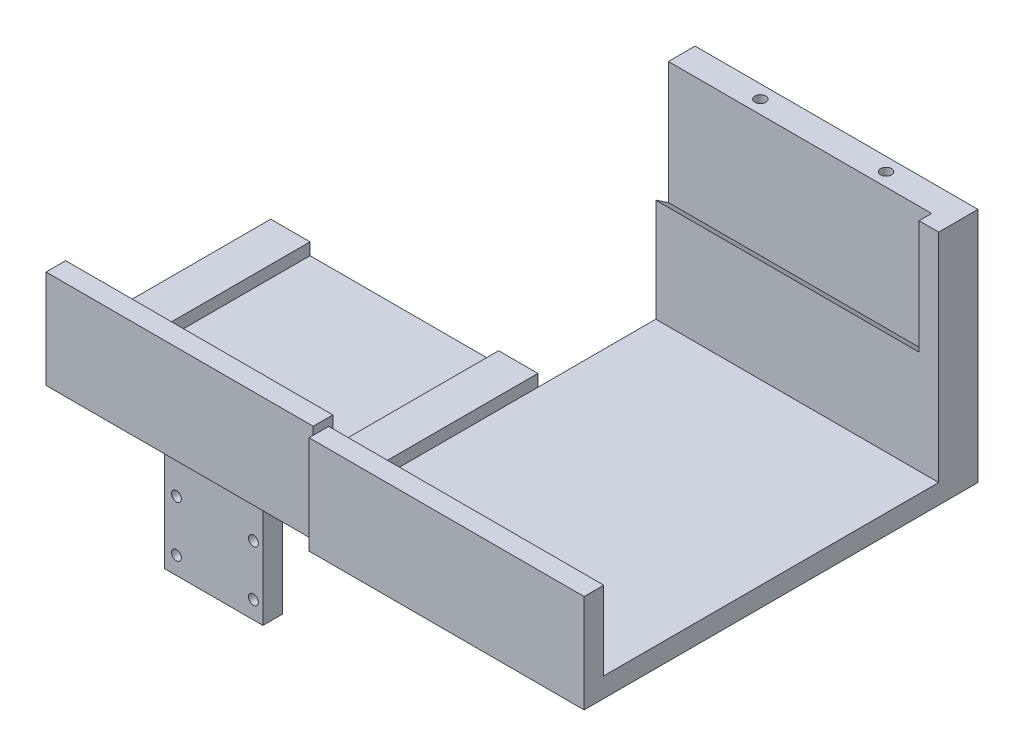
SolidWorks part; units mm, degrees
ref_plane "Front Plane" through (0, 0, 0) normal (0, 0, 1) x (1, 0, 0)
ref_plane "Top Plane" through (0, 0, 0) normal (0, 1, 0) x (1, 0, 0)
ref_plane "Right Plane" through (0, 0, 0) normal (1, 0, 0) x (0, 0, -1)
sketch "Sketch1" plane through (0, 0, 0) normal (0, 1, 0) x (1, 0, 0)
  line L1 (0, 0) -> (25, 0)
  line L2 (0, 0) -> (0, 38)
  line L3 (0, 38) -> (25, 38)
  line L4 (25, 0) -> (25, 38)
  dimension "D1" = 38
  dimension "D2" = 25
extrude "Boss-Extrude1" add sketch "Sketch1" along normal blind 12
ref_plane "Plane1" through (0, 0, -19) normal (0, 0, 1) x (1, 0, 0)
sketch "Sketch3" plane through (0, 0, 0) normal (0, 0, 1) x (1, 0, 0)
  line L1 (0, 12) -> (25, 12)
  line L2 (0, 12) -> (0, 0)
  line L3 (0, 0) -> (25, 0)
  line L4 (25, 12) -> (25, 0)
extrude "Boss-Extrude2" add sketch "Sketch3" along normal blind 5.5
sketch "Sketch5" plane through (0, 0, 0) normal (0, -1, 0) x (1, 0, 0)
  line L0 (25, 5.5) -> (25, -38) construction
  line L1 (0, 5.5) -> (25, 5.5)
  line L2 (0, 5.5) -> (0, 0.5)
  line L3 (0, 0.5) -> (25, 0.5)
  line L4 (25, 5.5) -> (25, 0.5)
  dimension "D1" = 5
extrude "Boss-Extrude3" add sketch "Sketch5" along normal blind 21
sketch "Sketch6" plane through (0, 0, 5.5) normal (0, 0, 1) x (1, 0, 0)
  line L0 (0, 12) -> (0, -21) construction
  line L2 (25, -21) -> (0, -21) construction
  circle A0 centre (3, -16.5) radius 1.25
  circle A1 centre (22.59, -16.5) radius 1.25
  circle A2 centre (22.59, -3.53) radius 1.25
  circle A3 centre (3, -3.53) radius 1.25
  dimension "D2" = 2.5
  dimension "D3" = 2.5
  dimension "D4" = 2.5
  dimension "D5" = 2.5
  dimension "D1" = 3
  dimension "D6" = 19.59
  dimension "D8" = 4.5
  dimension "D9" = 12.97
  dimension "D12" = 3
extrude "Cut-Extrude1" cut sketch "Sketch6" against normal blind 10
mirror "Mirror1" about plane through (0, 0, -19) normal (0, 0, 1) of "Cut-Extrude1", "Boss-Extrude3", "Boss-Extrude2"
sketch "Sketch7" plane through (0, 12, 0) normal (0, 1, 0) x (1, 0, 0)
  line L0 (12.5, 43.5) -> (12.5, -5.5) construction
  line L4 (0, 19) -> (25, 19) construction
  line L7 (117.5, 74) -> (-92.5, 74)
  line L8 (-92.5, 74) -> (-92.5, -11.25)
  line L9 (-92.5, -11.25) -> (117.5, -11.25)
  line L10 (117.5, -11.25) -> (117.5, 74)
  point P3 (12.5, -5.5)
  point P6 (12.5, 74)
  dimension "D1" = 55
  dimension "D2" = 30.25
  dimension "D3" = 210
extrude "Boss-Extrude4" add sketch "Sketch7" along normal blind 5
sketch "Sketch8" plane through (117.5, 0, 0) normal (1, 0, 0) x (0, 0, -1)
  line L0 (74, 12) -> (74, 72.2)
  line L2 (84, 72.2) -> (84, 12)
  line L3 (84, 12) -> (74, 12)
  line L4 (74, 72.2) -> (84, 72.2)
  dimension "D1" = 10
  dimension "D2" = 60.2
extrude "Boss-Extrude5" add sketch "Sketch8" against normal through all
sketch "Sketch9" plane through (-92.5, 0, 0) normal (-1, 0, 0) x (0, 0, 1)
  line L0 (-74, 43.24) -> (-77, 41.26) construction
  line L1 (-74, 72.2) -> (-74, 17) construction
  line L2 (-77, 41.26) -> (-77, 72.2) construction
  line L3 (-84, 72.2) -> (-74, 72.2) construction
  line L4 (-74, 17) -> (11.25, 17) construction
  line L5 (-74, 43.24) -> (-77.2, 41.128)
  line L6 (-77.2, 41.128) -> (-77.2, 72.2)
  line L7 (-77.2, 72.2) -> (-74, 72.2)
  line L8 (-74, 72.2) -> (-74, 43.24)
  dimension "D1" = 26.24
  dimension "D2" = 3
  dimension "D3" = 24.26
  dimension "D4" = 3.2
extrude "Cut-Extrude3" cut sketch "Sketch9" against normal through all
sketch "Sketch10" plane through (117.5, 0, 0) normal (1, 0, 0) x (0, 0, -1)
  line L0 (77.2, 72.2) -> (74, 72.2)
  line L1 (74, 72.2) -> (74, 43.24)
  line L2 (74, 43.24) -> (77.2, 41.128)
  line L3 (77.2, 41.128) -> (77.2, 72.2)
extrude "Boss-Extrude6" add sketch "Sketch10" against normal blind 5
sketch "Sketch11" plane through (0, 17, 0) normal (0, 1, 0) x (1, 0, 0)
  line L0 (117.5, 74) -> (-92.5, 74) construction
  line L1 (35.5, 74) -> (45.5, 74)
  line L2 (35.5, 74) -> (35.5, -11.25)
  line L3 (35.5, -11.25) -> (45.5, -11.25)
  line L4 (45.5, 74) -> (45.5, -11.25)
  line L5 (-92.5, -11.25) -> (117.5, -11.25) construction
  line L6 (117.5, -11.25) -> (117.5, 74) construction
  line L7 (-22.5, 74) -> (-12.5, 74)
  line L8 (-22.5, 74) -> (-22.5, -11.25)
  line L9 (-22.5, -11.25) -> (-12.5, -11.25)
  line L10 (-12.5, 74) -> (-12.5, -11.25)
  dimension "D1" = 72
  dimension "D2" = 10
  dimension "D3" = 68
  dimension "D4" = 10
extrude "Boss-Extrude7" add sketch "Sketch11" along normal blind 3.05
sketch "Sketch12" plane through (0, 17, 0) normal (0, 1, 0) x (1, 0, 0)
  line L0 (-92.5, 6.375) -> (-92.5, 56.375)
  line L1 (-92.5, 74) -> (-92.5, -11.25) construction
  line L2 (-92.5, 56.375) -> (-82.5, 56.375)
  line L3 (-82.5, 56.375) -> (-82.5, 6.375)
  line L4 (-82.5, 6.375) -> (-92.5, 6.375)
  line L5 (-42.5, 6.375) -> (-42.5, 56.375)
  line L6 (-42.5, 56.375) -> (-32.5, 56.375)
  line L7 (-32.5, 56.375) -> (-32.5, 6.375)
  line L8 (-32.5, 6.375) -> (-42.5, 6.375)
  line L9 (-92.5, 31.375) -> (74.7296, 31.375) construction
  line L10 (-22.5, 74) -> (-22.5, -11.25) construction
  point P5 (-92.5, 31.375)
  point P10 (-42.5, 31.375)
  dimension "D1" = 10
  dimension "D2" = 10
  dimension "D3" = 50
  dimension "D4" = 50
  dimension "D5" = 10
extrude "Boss-Extrude8" add sketch "Sketch12" along normal blind 10.45
sketch "Sketch13" plane through (0, 0, 11.25) normal (0, 0, 1) x (1, 0, 0)
  line L1 (117.5, 12) -> (47.5, 12)
  line L2 (117.5, 12) -> (117.5, 37)
  line L3 (117.5, 37) -> (47.5, 37)
  line L4 (47.5, 12) -> (47.5, 37)
  dimension "D1" = 70
  dimension "D2" = 25
extrude "Boss-Extrude9" add sketch "Sketch13" along normal blind 5
sketch "Sketch14" plane through (0, 0, 11.25) normal (0, 0, 1) x (1, 0, 0)
  line L0 (-92.5, 12) -> (47.5, 12) construction
  line L1 (45.5, 12) -> (-22.5, 12)
  line L2 (45.5, 12) -> (45.5, 37)
  line L3 (45.5, 37) -> (-22.5, 37)
  line L4 (-22.5, 12) -> (-22.5, 37)
  line L5 (47.5, 37) -> (47.5, 12) construction
  dimension "D1" = 68
  dimension "D2" = 2
  dimension "D3" = 25
extrude "Boss-Extrude10" add sketch "Sketch14" along normal blind 1.95 and the other way blind 3.05
sketch "Sketch16" plane through (0, 0, -84) normal (0, 0, -1) x (-1, 0, 0)
  line L0 (92.5, 72.2) -> (-117.5, 72.2) construction
  circle A0 centre (32.01, 72.2) radius 15
  dimension "D1" = 30
  dimension "D2" = 60.49
extrude "Cut-Extrude4" [suppressed] cut sketch "Sketch16" against normal up to surface (6.8 mm away)
sketch "Sketch17" [suppressed] plane through (0, 0, -84) normal (0, 0, -1) x (-1, 0, 0)
  line L1 (17.01, 72.2) -> (12.01, 72.2)
  line L2 (17.01, 72.2) -> (17.01, 82.2)
  line L3 (17.01, 82.2) -> (12.01, 82.2)
  line L4 (12.01, 72.2) -> (12.01, 82.2)
  dimension "D1" = 10
  dimension "D2" = 5
extrude "Boss-Extrude11" [suppressed] add sketch "Sketch17" against normal up to surface (6.8 mm away)
sketch "Sketch18" plane through (-92.5, 0, 0) normal (-1, 0, 0) x (0, 0, 1)
  line L1 (-84, 72.2) -> (11.25, 72.2)
  line L2 (-84, 72.2) -> (-84, 12)
  line L3 (-84, 12) -> (11.25, 12)
  line L4 (11.25, 72.2) -> (11.25, 12)
extrude "Cut-Extrude5" cut sketch "Sketch18" against normal up to surface (70 mm away) up to face at (-22.5, 21.5125, -10.3375)
sketch "Sketch19" plane through (0, 72.2, 0) normal (0, 1, 0) x (1, 0, 0)
  line L1 (-22.5, 84) -> (45.5, 84)
  line L2 (-22.5, 84) -> (-22.5, 44)
  line L3 (-22.5, 44) -> (45.5, 44)
  line L4 (45.5, 84) -> (45.5, 44)
  line L5 (45.5, -11.25) -> (45.5, 74) construction
  dimension "D1" = 40
extrude "Cut-Extrude6" cut sketch "Sketch19" against normal through all
sketch "Sketch20" plane through (0, 72.2, 0) normal (0, 1, 0) x (1, 0, 0)
  line L0 (45.5, 80.6) -> (117.5, 80.6) construction
  line L1 (45.5, 77.2) -> (45.5, 84) construction
  line L2 (117.5, 84) -> (117.5, 74) construction
  circle A0 centre (65.5, 80.6) radius 1.3891
  circle A1 centre (97.5, 80.6) radius 1.3891
  dimension "D1" = 2.7781
  dimension "D2" = 2.7781
  dimension "D3" = 20
  dimension "D4" = 20
extrude "Cut-Extrude7" cut sketch "Sketch20" against normal blind 10
